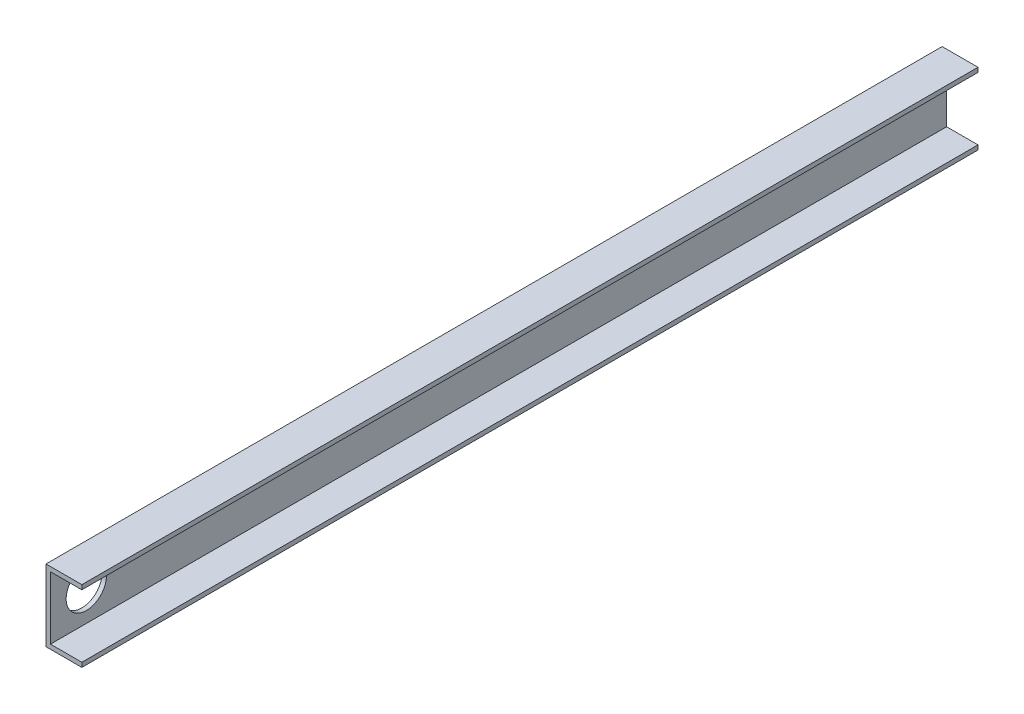
SolidWorks part; units mm, degrees
ref_plane "Front Plane" through (0, 0, 0) normal (0, 0, 1) x (1, 0, 0)
ref_plane "Top Plane" through (0, 0, 0) normal (0, 1, 0) x (1, 0, 0)
ref_plane "Right Plane" through (0, 0, 0) normal (1, 0, 0) x (0, 0, -1)
sketch "Sketch1" plane through (0, 0, 0) normal (0, 0, 1) x (1, 0, 0)
  line L0 (0, 0) -> (0, 50.8)
  line L1 (0, 50.8) -> (25.4, 50.8)
  line L2 (25.4, 50.8) -> (25.4, 47.625)
  line L3 (25.4, 47.625) -> (3.175, 47.625)
  line L4 (3.175, 47.625) -> (3.175, 3.175)
  line L5 (3.175, 3.175) -> (25.4, 3.175)
  line L6 (25.4, 3.175) -> (25.4, 0)
  line L7 (25.4, 0) -> (0, 0)
  dimension "D1" = 50.8
  dimension "D2" = 25.4
  dimension "D3" = 3.175
  dimension "D4" = 3.175
  dimension "D5" = 3.175
  dimension "D6" = 25.4
extrude "Boss-Extrude1" add sketch "Sketch1" along normal blind 635
sketch "Sketch2" plane through (0, 0, 0) normal (-1, 0, 0) x (0, 0, 1)
  line L0 (635, 0) -> (0, 0) construction
  line L2 (635, 50.8) -> (635, 0) construction
  circle A0 centre (609.6, 25.4) radius 14.2875
  dimension "D1" = 28.575
  dimension "D3" = 25.4
  dimension "D2" = 25.4
extrude "Cut-Extrude1" cut sketch "Sketch2" against normal through all
